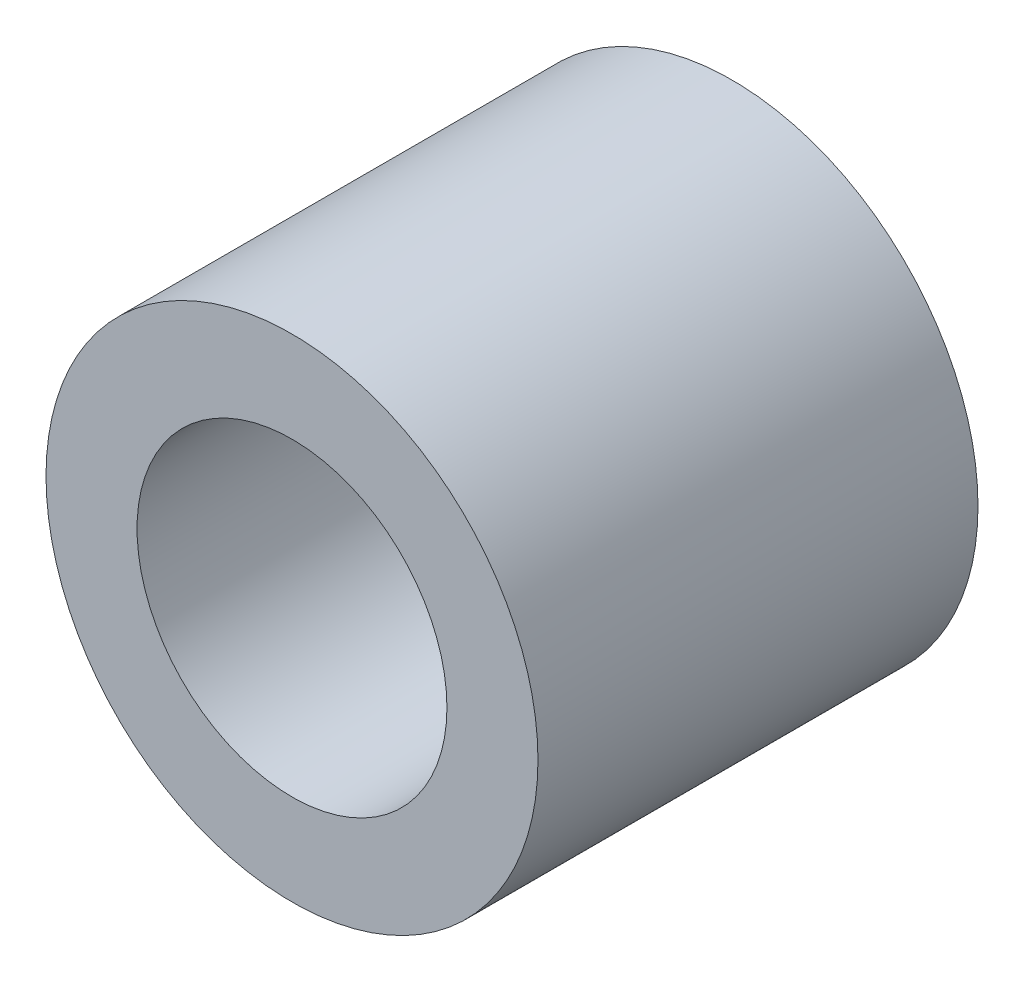
SolidWorks part; units mm, degrees
material "ABS"
ref_plane "Front Plane" through (0, 0, 0) normal (0, 0, 1) x (1, 0, 0)
ref_plane "Top Plane" through (0, 0, 0) normal (0, 1, 0) x (1, 0, 0)
ref_plane "Right Plane" through (0, 0, 0) normal (1, 0, 0) x (0, 0, -1)
sketch "Sketch1" plane through (0, 0, 0) normal (0, 0, 1) x (1, 0, 0)
  circle A0 centre (0, 0) radius 1.6
  circle A1 centre (0, 0) radius 2.54
  dimension "D1" = 3.2
  dimension "D2" = 5.08
extrude "Boss-Extrude1" add sketch "Sketch1" along normal mid plane 4.5435
